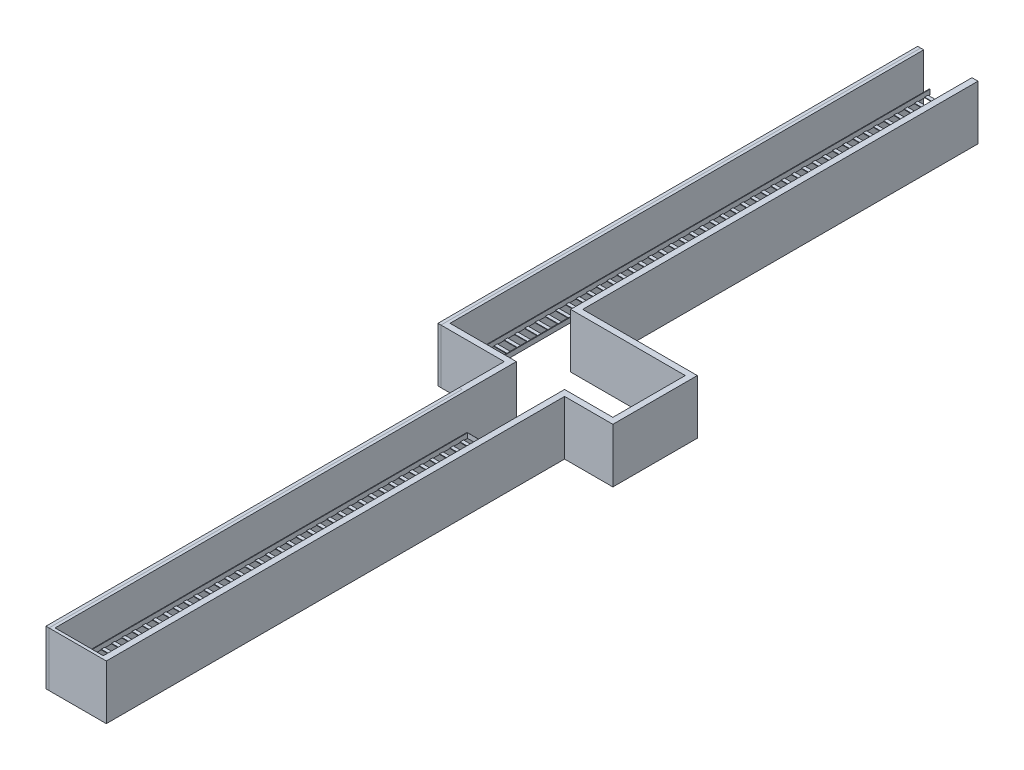
SolidWorks part; units mm, degrees
ref_plane "Alzado" through (0, 0, 0) normal (0, 0, 1) x (1, 0, 0)
ref_plane "Planta" through (0, 0, 0) normal (0, 1, 0) x (1, 0, 0)
ref_plane "Vista lateral" through (0, 0, 0) normal (1, 0, 0) x (0, 0, -1)
sketch "Croquis1" plane through (0, 0, 0) normal (0, 1, 0) x (1, 0, 0)
  line L0 (1099.5, -7450) -> (499.5, -7450)
  line L1 (499.5, -7450) -> (499.5, -600)
  line L2 (499.5, -600) -> (-75, -600)
  line L3 (-75, -600) -> (-600, -600)
  line L4 (-600, -600) -> (-600, 8600)
  line L5 (-600, 8600) -> (0, 8600)
  line L6 (0, 8600) -> (0, 0)
  line L7 (0, 0) -> (1099.5, 0)
  line L8 (1099.5, 0) -> (1099.5, -7450)
  line L9 (1049.5, -50) -> (1049.5, -7400)
  line L10 (1049.5, -7400) -> (549.5, -7400)
  line L11 (549.5, -7400) -> (549.5, -550)
  line L12 (549.5, -550) -> (-75, -550)
  line L13 (-75, -550) -> (-550, -550)
  line L14 (-550, -550) -> (-550, 8550)
  line L15 (-550, 8550) -> (-50, 8550)
  line L16 (-50, 8550) -> (-50, -50)
  line L17 (-50, -50) -> (1049.5, -50)
  dimension "D1" = 600
  dimension "D2" = 600
  dimension "D3" = 9200
  dimension "D4" = 7450
  dimension "D5" = 1099.5
  dimension "D6" = 600
  dimension "D7" = 50
extrude "Saliente-Extruir1" add sketch "Croquis1" along normal blind 900
sketch "Croquis2" plane through (0, 900, 0) normal (0, 1, 0) x (1, 0, 0)
  line L0 (-600, -600) -> (100, -600)
  line L1 (-600, -600) -> (499.5, -600) construction
  line L2 (100, -600) -> (100, 100)
  line L3 (100, 100) -> (-600, 100)
  line L4 (-600, 8600) -> (-600, -600) construction
  line L5 (-600, 100) -> (-600, -600)
  dimension "D1" = 700
  dimension "D2" = 700
extrude "Cortar-Extruir1" cut sketch "Croquis2" against normal blind 900
ref_plane "Plano1" through (799.5, 0, 0) normal (1, 0, 0) x (0, 0, -1)
sketch "Croquis4" plane through (0, 0, -8550) normal (0, 0, 1) x (1, 0, 0)
  line L0 (-300, 0) -> (-300, 350) construction
  line L1 (-50, 0) -> (-550, 0) construction
  line L3 (-452.4, 390) -> (-147.6, 390)
  line L4 (-452.4, 390) -> (-452.4, 310)
  line L5 (-452.4, 310) -> (-147.6, 310)
  line L6 (-147.6, 390) -> (-147.6, 310)
  line L7 (-452.4, 390) -> (-147.6, 310) construction
  line L8 (-452.4, 310) -> (-147.6, 390) construction
  dimension "D1" = 350
  dimension "D2" = 304.8
  dimension "D3" = 80
extrude "Saliente-Extruir2" add sketch "Croquis4" along normal up to surface (8450 mm away) up to face at (-575, 450, -100)
sketch "Croquis5" plane through (0, 0, -100) normal (0, 0, 1) x (1, 0, 0)
  line L0 (-452.4, 390) -> (-452.4, 310)
  line L1 (-452.4, 310) -> (-147.6, 310)
  line L2 (-147.6, 310) -> (-147.6, 390)
  line L3 (-147.6, 390) -> (-157.6, 390)
  line L4 (-452.4, 390) -> (-147.6, 390) construction
  line L5 (-157.6, 390) -> (-157.6, 320)
  line L6 (-157.6, 320) -> (-442.4, 320)
  line L7 (-442.4, 320) -> (-442.4, 390)
  line L8 (-147.6, 390) -> (-452.4, 390) construction
  line L9 (-442.4, 390) -> (-452.4, 390)
  line L10 (-442.4, 390) -> (-157.6, 390)
  line M7 (-147.6, 390) -> (-452.4, 390)
  dimension "D1" = 10
  dimension "D2" = 10
  dimension "D3" = 10
extrude "Cortar-Extruir2" cut sketch "Croquis5" against normal up to surface (8450 mm away) contours L7 L6 L5 M7 up to face at (-300, 450, -8550)
sketch "Croquis6" plane through (0, 320, 0) normal (0, 1, 0) x (1, 0, 0)
  line L0 (-442.4, 8550) -> (-442.4, 100) construction
  line L1 (-157.6, 8518.5389) -> (-442.4, 8518.5389)
  line L2 (-157.6, 8518.5389) -> (-157.6, 8403.5389)
  line L3 (-157.6, 8403.5389) -> (-442.4, 8403.5389)
  line L4 (-442.4, 8518.5389) -> (-442.4, 8403.5389)
  line L5 (-157.6, 8518.5389) -> (-442.4, 8403.5389) construction
  line L6 (-157.6, 8403.5389) -> (-442.4, 8518.5389) construction
  line L7 (-157.6, 8550) -> (-157.6, 100) construction
  point P0 (-300, 8461.0389)
  dimension "D1" = 115
extrude "Cortar-Extruir3" cut sketch "Croquis6" against normal blind 20
pattern_linear "MatrizL1" count 49 spacing 170 along (0, 0, 1) of "Cortar-Extruir3"
sketch "Croquis7" plane through (0, 0, 7400) normal (0, 0, -1) x (-1, 0, 0)
  line L0 (-1099.5, 0) -> (-499.5, 0) construction
  line L1 (-499.5, 0) -> (-799.5, 0) construction
  line L2 (-799.5, 0) -> (-799.5, 350) construction
  line L3 (-799.5, 55) -> (-799.5, -55) construction
  line L5 (-951.9, 390) -> (-647.1, 390)
  line L6 (-951.9, 390) -> (-951.9, 310)
  line L7 (-951.9, 310) -> (-647.1, 310)
  line L8 (-647.1, 390) -> (-647.1, 310)
  line L9 (-951.9, 390) -> (-647.1, 310) construction
  line L10 (-951.9, 310) -> (-647.1, 390) construction
  dimension "D1" = 350
  dimension "D2" = 304.8
  dimension "D3" = 80
extrude "Saliente-Extruir3" add sketch "Croquis7" along normal blind 6730
sketch "Croquis8" plane through (0, 0, 670) normal (0, 0, -1) x (-1, 0, 0)
  line L0 (-951.9, 390) -> (-941.9, 390) construction
  line L1 (-647.1, 390) -> (-951.9, 390) construction
  line L2 (-941.9, 390) -> (-941.9, 320)
  line L3 (-941.9, 320) -> (-657.1, 320)
  line L4 (-657.1, 320) -> (-657.1, 390)
  line L5 (-657.1, 390) -> (-941.9, 390)
  line L6 (-951.9, 390) -> (-951.9, 310) construction
  line L7 (-951.9, 310) -> (-647.1, 310) construction
  line L8 (-647.1, 310) -> (-647.1, 390) construction
  dimension "D1" = 10
  dimension "D2" = 10
  dimension "D3" = 10
extrude "Cortar-Extruir4" cut sketch "Croquis8" against normal up to surface (6730 mm away) up to face at (799.5, 450, 7400)
sketch "Croquis9" plane through (0, 320, 0) normal (0, 1, 0) x (1, 0, 0)
  line L0 (799.5, -55) -> (799.5, 55) construction
  line L1 (657.1, -7366.8108) -> (941.9, -7366.8108)
  line L2 (657.1, -7366.8108) -> (657.1, -7251.8108)
  line L3 (657.1, -7251.8108) -> (941.9, -7251.8108)
  line L4 (941.9, -7366.8108) -> (941.9, -7251.8108)
  line L5 (657.1, -7366.8108) -> (941.9, -7251.8108) construction
  line L6 (657.1, -7251.8108) -> (941.9, -7366.8108) construction
  line L7 (941.9, -7400) -> (941.9, -670) construction
  point P0 (799.5, -7309.3108)
  dimension "D1" = 115
extrude "Cortar-Extruir5" cut sketch "Croquis9" against normal blind 10
pattern_linear "MatrizL2" count 40 spacing 170 along (0, 0, -1) of "Cortar-Extruir5"
sketch "Croquis12" plane through (0, 0, 670) normal (0, 0, -1) x (-1, 0, 0)
  line L0 (-941.9, 390) -> (-647.1, 390)
  line L1 (-647.1, 390) -> (-647.1, 310)
  line L2 (-647.1, 310) -> (-951.9, 310)
  line L3 (-951.9, 310) -> (-951.9, 390)
  line L4 (-951.9, 390) -> (-941.9, 390)
extrude "Saliente-Extruir4" add sketch "Croquis12" along normal blind 2
sketch "Croquis18" plane through (0, 900, 0) normal (0, 1, 0) x (1, 0, 0)
  line L0 (-600, 8600) -> (-650, 8600)
  line L1 (-650, 8600) -> (-650, 100)
  line L2 (-600, 100) -> (-650, 100)
  line L4 (-600, 100) -> (-600, 8600)
  line L5 (0, 8600) -> (50, 8600)
  line L6 (50, 8600) -> (50, 100)
  line L7 (0, 100) -> (50, 100)
  line L8 (0, 100) -> (0, 8600)
  line L9 (100, 0) -> (100, 50)
  line L10 (100, 50) -> (1149.5, 50)
  line L11 (1149.5, 50) -> (1149.5, -7450)
  line L12 (1099.5, -7450) -> (1149.5, -7450)
  line L13 (1099.5, -7450) -> (1099.5, 0)
  line L14 (1099.5, 0) -> (100, 0)
  line L15 (100, -600) -> (100, -650)
  line L16 (100, -650) -> (449.5, -650)
  line L17 (449.5, -650) -> (449.5, -7450)
  line L18 (449.5, -7450) -> (499.5, -7450)
  line L19 (499.5, -7450) -> (499.5, -600)
  line L20 (499.5, -600) -> (100, -600)
  dimension "D1" = 50
  dimension "D2" = 50
  dimension "D3" = 50
  dimension "D4" = 50
  dimension "D5" = 50
  dimension "D6" = 50
extrude "Saliente-Extruir5" add sketch "Croquis18" against normal blind 900 separate body
sketch "Croquis76" plane through (50, 0, 0) normal (1, 0, 0) x (0, 0, -1)
  line L0 (50, 0) -> (1547, 0)
  line L1 (100, 0) -> (8600, 0) construction
  line L2 (1547, 0) -> (1547, 900)
  line L3 (100, 900) -> (8600, 900) construction
  line L4 (1547, 900) -> (50, 900)
  line L5 (50, 900) -> (50, 0)
  dimension "D1" = 1497
extrude "Saliente-Extruir26" add sketch "Croquis76" along normal blind 2200
sketch "Croquis78" plane through (0, 0, -1547) normal (0, 0, -1) x (-1, 0, 0)
  line L0 (-50, 900) -> (-350, 900)
  line L1 (-2250, 900) -> (-50, 900) construction
  line L2 (-350, 900) -> (-350, 0)
  line L3 (-350, 0) -> (-50, 0)
  line L4 (-50, 0) -> (-50, 900)
  dimension "D1" = 300
extrude "Saliente-Extruir27" add sketch "Croquis78" along normal up to surface (7053 mm away) up to face at (25, 450, -8600)
sketch "Croquis79" plane through (0, 0, -50) normal (0, 0, 1) x (1, 0, 0)
  line L0 (1149.5, 900) -> (1449.5, 900)
  line L1 (1149.5, 900) -> (1149.5, 0)
  line L2 (1149.5, 0) -> (1449.5, 0)
  line L3 (2250, 0) -> (1149.5, 0) construction
  line L4 (1449.5, 0) -> (1449.5, 900)
  dimension "D1" = 300
extrude "Saliente-Extruir28" add sketch "Croquis79" along normal up to surface (7500 mm away) up to face at (1124.5, 450, 7450)
sketch "Croquis80" plane through (0, 0, 0) normal (0, -1, 0) x (1, 0, 0)
  line L0 (-50, -8550) -> (250, -8550)
  line L1 (250, -8550) -> (250, -1447)
  line L2 (250, -1447) -> (2150, -1447)
  line L3 (2150, -1447) -> (2150, -150)
  line L4 (2150, -150) -> (1349.5, -150)
  line L5 (1349.5, -150) -> (1349.5, 7400)
  line L6 (1349.5, 7400) -> (1049.5, 7400)
  line L7 (1049.5, 7400) -> (1049.5, 50)
  line L8 (1049.5, 50) -> (100, 50)
  line L9 (100, 50) -> (100, -50)
  line L10 (100, -50) -> (50, -50)
  line L11 (50, -50) -> (50, -100)
  line L12 (50, -100) -> (-50, -100)
  line L13 (-50, -100) -> (-50, -8550)
  line L14 (350, -8600) -> (350, -1547) construction
  line L15 (2250, -1547) -> (350, -1547) construction
  line L16 (2250, -50) -> (2250, -1547) construction
  line L17 (2250, -50) -> (1449.5, -50) construction
  line L18 (1449.5, 7450) -> (1449.5, -50) construction
  dimension "D1" = 100
  dimension "D2" = 100
  dimension "D3" = 100
  dimension "D4" = 100
  dimension "D5" = 100
extrude "Cortar-Extruir19" cut sketch "Croquis80" against normal blind 900
sketch "Croquis85" plane through (2250, 0, 0) normal (1, 0, 0) x (0, 0, -1)
  line L0 (50, 0) -> (147, 0)
  line L1 (50, 0) -> (1547, 0) construction
  line L2 (147, 0) -> (147, 900)
  line L3 (1547, 900) -> (50, 900) construction
  line L4 (147, 900) -> (50, 900)
  line L5 (50, 900) -> (50, 0)
  line L6 (1547, 0) -> (1547, 900) construction
  dimension "D1" = 1400
extrude "Cortar-Extruir21" cut sketch "Croquis85" against normal up to surface (800.5 mm away) up to face at (1449.5, 450, 3700)
sketch "Croquis86" plane through (2150, 0, 0) normal (-1, 0, 0) x (0, 0, 1)
  line L0 (-150, 0) -> (-150, 900)
  line L1 (-150, 900) -> (-247, 900)
  line L2 (-1447, 900) -> (-150, 900) construction
  line L3 (-247, 900) -> (-247, 0)
  line L4 (-1447, 0) -> (-150, 0) construction
  line L5 (-247, 0) -> (-150, 0)
  dimension "D1" = 97
extrude "Saliente-Extruir31" add sketch "Croquis86" along normal up to surface (800.5 mm away) up to face at (1349.5, 450, 3625)
sketch "Croquis87" plane through (0, 0, 550) normal (0, 0, -1) x (-1, 0, 0)
  line L0 (-549.5, 900) -> (-449.5, 900)
  line L1 (-100, 900) -> (-549.5, 900) construction
  line L2 (-549.5, 900) -> (-549.5, 0)
  line L3 (-549.5, 0) -> (-449.5, 0)
  line L4 (-100, 0) -> (-549.5, 0) construction
  line L5 (-449.5, 0) -> (-449.5, 900)
  dimension "D1" = 100
extrude "Saliente-Extruir32" add sketch "Croquis87" along normal up to surface (797 mm away) up to face at (1749.75, 450, -247)
sketch "Croquis88" plane through (100, 0, 0) normal (-1, 0, 0) x (0, 0, 1)
  line L0 (550, 900) -> (650, 900)
  line L1 (650, 900) -> (650, 0)
  line L2 (650, 0) -> (550, 0)
  line L3 (550, 0) -> (550, 900)
extrude "Cortar-Extruir22" cut sketch "Croquis88" against normal up to surface (349.5 mm away) up to face at (449.5, 450, 4050)
sketch "Croquis89" plane through (449.5, 0, 0) normal (-1, 0, 0) x (0, 0, 1)
  line L0 (-247, 900) -> (-147, 900)
  line L1 (-147, 900) -> (-147, 0)
  line L2 (-147, 0) -> (-247, 0)
  line L3 (-247, 0) -> (-247, 900)
extrude "Saliente-Extruir33" add sketch "Croquis89" along normal up to surface (999.5 mm away) up to face at (-550, 450, -4325)
sketch "Croquis90" plane through (-550, 0, 0) normal (1, 0, 0) x (0, 0, -1)
  line L0 (147, 900) -> (147, 0)
  line L2 (147, 0) -> (88.573, 0)
  line L3 (88.573, 0) -> (88.573, 900)
  line L4 (88.573, 900) -> (147, 900)
extrude "Cortar-Extruir23" cut sketch "Croquis90" against normal mid plane 1000
sketch "Croquis91" plane through (0, 0, -8600) normal (0, 0, -1) x (-1, 0, 0)
  line L0 (-350, 900) -> (650, 900)
  line L1 (650, 900) -> (650, 0)
  line L2 (650, 0) -> (-350, 0)
  line L3 (-350, 0) -> (-350, 900)
extrude "Cortar-Extruir24" cut sketch "Croquis91" against normal blind 500
